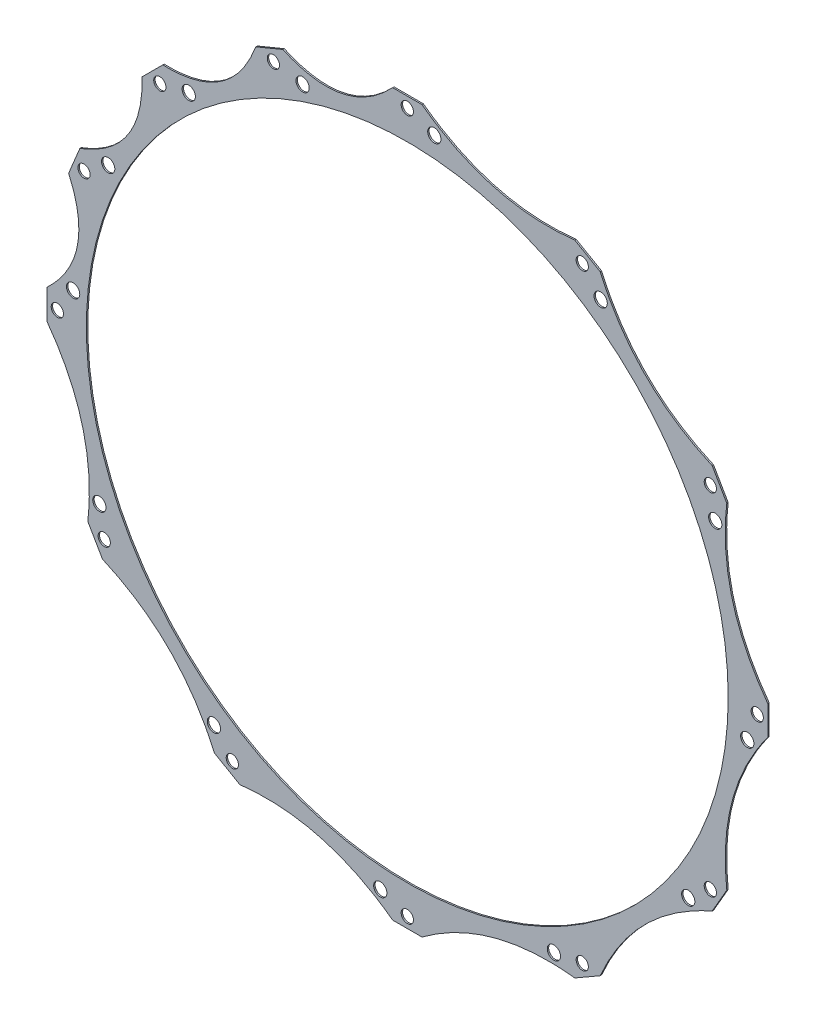
SolidWorks part; units mm, degrees
other "3"
other "2"
other "1"
other "4"
material "Maple"
ref_plane "Wasteboard" through (0, 0, 0) normal (0, 0, 1) x (1, 0, 0)
ref_plane "Left-Right" through (0, 0, 0) normal (0, 1, 0) x (1, 0, 0)
ref_plane "Front-Back" through (0, 0, 0) normal (1, 0, 0) x (0, 0, -1)
sketch "Sketch2" plane through (0, 0, 0) normal (0, 0, 1) x (1, 0, 0)
  line L0 (0, 0) -> (0, 50000) construction
  circle A0 centre (0, 0) radius 192.8812 construction
  circle A1 centre (0, 0) radius 209.55 construction
  circle A2 centre (0, 0) radius 172.72 construction
  circle A3 centre (0, 0) radius 252.73 construction
  circle A4 centre (0, 0) radius 184.785 construction
  circle A5 centre (0, 0) radius 190.5
  circle A6 centre (0, 0) radius 169.4688
  circle A7 centre (0, 0) radius 194.31 construction
  circle A8 centre (0, 184.785) radius 9.525 construction
  point P14 (0, 172.72)
  point P15 (0, 169.4688)
  point P16 (0, 175.26)
  point P17 (0, 0)
  dimension "D1" = 385.7625
  dimension "D2" = 419.1
  dimension "D3" = 2.54
  dimension "D4" = 505.46
  dimension "D5" = 369.57
  dimension "D6" = 381
  dimension "D7" = 3.2512
  dimension "D8" = 388.62
  dimension "D9" = 19.05
sketch "Sketch4" plane through (0, 0, 0) normal (0, 0, 1) x (1, 0, 0)
  line L0 (92.3925, 160.0285) -> (0, 184.785) construction
  line L1 (46.1963, 172.4068) -> (-12894.756, -48123.8846) construction
  line L2 (-7.7353, 190.3429) -> (7.7353, 190.3429)
  line L6 (-160.9741, -101.8704) -> (-168.7094, -88.4724)
  line L7 (-88.4724, -168.7094) -> (-101.8704, -160.9741)
  line L8 (7.7353, -190.3429) -> (-7.7353, -190.3429)
  line L9 (101.8704, -160.9741) -> (88.4724, -168.7094)
  line L10 (168.7094, -88.4724) -> (160.9741, -101.8704)
  line L11 (190.3429, 7.7353) -> (190.3429, -7.7353)
  line L12 (160.9741, 101.8704) -> (168.7094, 88.4724)
  line L13 (88.4724, 168.7094) -> (101.8704, 160.9741)
  line L14 (-101.8704, 160.9741) -> (-88.4724, 168.7094) [skipped]
  line L15 (-168.7094, 88.4724) -> (-160.9741, 101.8704) [skipped]
  line L16 (-79.9876, 172.8937) -> (-65.6945, 178.8141)
  line L17 (-70.7142, 170.7191) -> (0, 184.785) construction
  line L18 (-35.3571, 177.752) -> (9719.159, -48861.512) construction
  line L19 (-140.0625, 129.123) -> (-129.123, 140.0625)
  line L20 (-178.8141, 65.6945) -> (-172.8937, 79.9876)
  line L21 (-190.3429, -7.7353) -> (-190.3429, 7.7353)
  line L23 (-172.8937, -79.9876) -> (-178.8141, -65.6945) [skipped]
  line L24 (-190.3429, -7.7353) -> (-190.3429, 7.7353) [skipped]
  circle A0 centre (0, 184.785) radius 3.175 construction
  circle A1 centre (0, 184.785) radius 9.525 construction
  circle A2 centre (0, 184.785) radius 9.525 construction
  circle A3 centre (0, 0) radius 177.6413 construction
  circle A4 centre (0, 0) radius 190.5 construction
  circle A5 centre (0, 0) radius 184.785 construction
  circle A6 centre (0, 0) radius 169.4688 construction
  circle A7 centre (0, 0) radius 169.4688
  circle A8 centre (92.3925, 160.0285) radius 9.525 construction
  circle A9 centre (0, 0) radius 192.8812 construction
  circle A10 centre (0, 184.785) radius 3.2385
  circle A14 centre (-160.0285, -92.3925) radius 3.2385
  circle A15 centre (-92.3925, -160.0285) radius 3.2385
  circle A16 centre (0, -184.785) radius 3.2385
  circle A17 centre (92.3925, -160.0285) radius 3.2385
  circle A18 centre (160.0285, -92.3925) radius 3.2385
  circle A19 centre (184.785, 0) radius 3.2385
  circle A20 centre (160.0285, 92.3925) radius 3.2385
  circle A21 centre (92.3925, 160.0285) radius 3.2385
  circle A22 centre (-160.0285, 92.3925) radius 3.2385 [skipped]
  circle A23 centre (-92.3925, 160.0285) radius 3.2385 [skipped]
  circle A24 centre (-70.7142, 170.7191) radius 9.525 construction
  circle A25 centre (-130.6627, 130.6627) radius 9.525 construction
  circle A26 centre (-170.7191, 70.7142) radius 9.525 construction
  circle A27 centre (-184.785, 0) radius 9.525 construction
  circle A28 centre (-70.7142, 170.7191) radius 3.2385
  circle A29 centre (-130.6627, 130.6627) radius 3.2385
  circle A30 centre (-170.7191, 70.7142) radius 3.2385
  circle A31 centre (-184.785, 0) radius 3.2385
  circle A32 centre (-184.785, 0) radius 3.2385 [skipped]
  spline S0 degree 2 poles (7.7353, 190.3429) (43.85, 163.6504) (88.4724, 168.7094) knots 0 0 0 1 1 1
  spline S1 degree 2 poles (-65.6945, 178.8141) (-32.5972, 163.8774) (-7.7353, 190.3429) knots 0 0 0 1 1 1
  spline S2 degree 2 poles (-129.123, 140.0625) (-92.8291, 138.9285) (-79.9876, 172.8937) knots 0 0 0 1 1 1
  spline S3 degree 2 poles (-172.8937, 79.9876) (-138.9285, 92.8291) (-140.0625, 129.123) knots 0 0 0 1 1 1
  spline S4 degree 2 poles (-168.7094, -88.4724) (-163.6504, -43.85) (-190.3429, -7.7353) knots 0 0 0 1 1 1
  spline S5 degree 2 poles (-101.8704, -160.9741) (-119.8004, -119.8004) (-160.9741, -101.8704) knots 0 0 0 1 1 1
  spline S6 degree 2 poles (-7.7353, -190.3429) (-43.85, -163.6504) (-88.4724, -168.7094) knots 0 0 0 1 1 1
  spline S7 degree 2 poles (88.4724, -168.7094) (43.85, -163.6504) (7.7353, -190.3429) knots 0 0 0 1 1 1
  spline S8 degree 2 poles (160.9741, -101.8704) (119.8004, -119.8004) (101.8704, -160.9741) knots 0 0 0 1 1 1
  spline S9 degree 2 poles (190.3429, -7.7353) (163.6504, -43.85) (168.7094, -88.4724) knots 0 0 0 1 1 1
  spline S10 degree 2 poles (168.7094, 88.4724) (163.6504, 43.85) (190.3429, 7.7353) knots 0 0 0 1 1 1
  spline S11 degree 2 poles (101.8704, 160.9741) (119.8004, 119.8004) (160.9741, 101.8704) knots 0 0 0 1 1 1
  spline S12 degree 2 poles (-190.3429, 7.7353) (-163.8774, 32.5972) (-178.8141, 65.6945) knots 0 0 0 1 1 1
  point P6 (0, 0)
  point P18 (0, 0)
  point P19 (0, 0)
  point P21 (0, 0)
  point P24 (45.9769, 171.5883)
  point P29 (46.1963, 172.4068)
  point P31 (-7.7353, 190.3429)
  point P33 (-79.9876, 172.8937)
  point P34 (-65.6945, 178.8141)
  point P45 (0, 0)
  point P48 (-34.6561, 174.2279)
  point P103 (0, 0)
  point P112 (-35.3571, 177.752)
  point P123 (0, 0)
  point P126 (0, 0)
  dimension "D1" = 6.35
  dimension "D2" = 19.05
  dimension "D3" = 15.24
  dimension "D6" = 6.477
  dimension "D7" = 12
  dimension "D4" = 2
  dimension "D5" = 2
  dimension "D8" = 5
  dimension "D9" = 5
extrude "Boss-Extrude2" add sketch "Sketch4" along normal blind 0.75
sketch "Sketch6" plane through (0, 0, 0.75) normal (0, 0, 1) x (1, 0, 0)
  line L0 (0, -200000) -> (0, 250000) construction
  circle A0 centre (14.2615, 179.5235) radius 3.5
  circle A1 centre (0, 184.785) radius 3.2385 construction
  circle A2 centre (-176.4553, 13.2615) radius 3.5
  circle A3 centre (-184.785, 0) radius 3.2385 construction
  circle A4 centre (-184.785, 0) radius 3.2385
  point P2 (-3.2385, 184.785)
  point P3 (17.7615, 179.5235)
  point P6 (14.2615, 176.0235)
  point P7 (0, 188.0235)
  point P8 (-176.4553, 16.7615)
  point P11 (-184.785, -3.2385)
  point P12 (-173.0235, 12.5739)
  point P18 (-188.0235, 0)
  point P20 (0, 0)
  point P21 (0, 0)
  point P22 (0, 0)
  point P23 (-174.0985, 8.5126)
  point P24 (-178.2218, 12.2129)
  dimension "D1" = 21
  dimension "D3" = 7
  dimension "D4" = 20
  dimension "D6" = 7
  dimension "D2" = 12
  dimension "D5" = 15
sketch "Sketch8" plane through (0, 0, 0.75) normal (0, 0, 1) x (1, 0, 0)
  line L0 (0, 0) -> (22.9876, 289.3677) construction
  line L1 (0, 0) -> (102.1126, 148.3412) construction
  line L2 (0, 0) -> (-176.4553, 13.2615) construction
  line L3 (0, 0) -> (-157.9485, 79.7785) construction
  circle A0 centre (14.2615, 179.5235) radius 3.5 construction
  circle A1 centre (14.2615, 179.5235) radius 3.5
  circle A2 centre (-176.4553, 13.2615) radius 3.5 construction
  circle A3 centre (-176.4553, 13.2615) radius 3.5
  circle A4 centre (102.1126, 148.3412) radius 3.5
  circle A5 centre (162.6027, 77.4109) radius 3.5
  circle A6 centre (179.5235, -14.2615) radius 3.5
  circle A7 centre (148.3412, -102.1126) radius 3.5
  circle A8 centre (77.4109, -162.6027) radius 3.5
  circle A9 centre (-14.2615, -179.5235) radius 3.5
  circle A10 centre (-102.1126, -148.3412) radius 3.5
  circle A11 centre (-162.6027, -77.4109) radius 3.5
  circle A12 centre (-157.9485, 79.7785) radius 3.5
  circle A13 centre (-115.3954, 134.15) radius 3.5
  circle A14 centre (-55.2745, 168.0984) radius 3.5
  point P6 (0, 0)
  point P28 (0, 0)
  point P29 (0, 0)
  dimension "D1" = 30
  dimension "D2" = 22.5
extrude "Cut-Extrude2" cut sketch "Sketch8" against normal through all
sketch "Sketch5" plane through (0, 0, 0.75) normal (0, 0, 1) x (1, 0, 0)
  line L0 (-161.9497, -16.9673) -> (-174.9303, -18.3273)
  line L1 (-174.9303, -18.3273) -> (-175.7387, -10.6112)
  line L2 (-175.7387, -10.6112) -> (-198.2442, -12.969)
  line L3 (-16.9673, 161.9497) -> (-18.3273, 174.9303)
  line L4 (-18.3273, 174.9303) -> (-10.6112, 175.7387)
  line L5 (-10.6112, 175.7387) -> (-12.969, 198.2442)
  line L6 (16.9673, -161.9497) -> (18.3273, -174.9303)
  line L7 (18.3273, -174.9303) -> (10.6112, -175.7387)
  line L8 (10.6112, -175.7387) -> (12.969, -198.2442)
  line L9 (161.9497, 16.9673) -> (174.9303, 18.3273)
  line L10 (174.9303, 18.3273) -> (175.7387, 10.6112)
  line L11 (175.7387, 10.6112) -> (198.2442, 12.969)
  point P19 (0, 0)
  dimension "D1" = 4
split "Split1" bodies to split 141 resulting bodies 137 138 139 140
